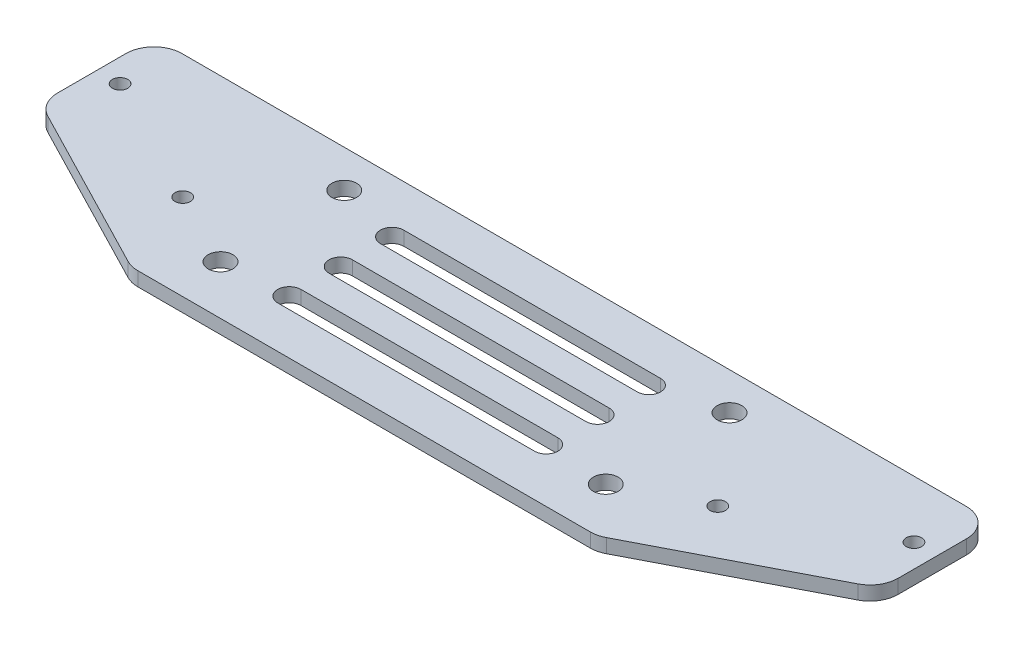
SolidWorks part; units mm, degrees
material "A-玻璃纤维"
ref_plane "前视基准面" through (0, 0, 0) normal (0, 0, 1) x (1, 0, 0)
ref_plane "上视基准面" through (0, 0, 0) normal (0, 1, 0) x (1, 0, 0)
ref_plane "右视基准面" through (0, 0, 0) normal (1, 0, 0) x (0, 0, -1)
sketch "草图1" plane through (0, 0, 0) normal (0, 1, 0) x (1, 0, 0)
  line L0 (0, 13.25) -> (0, -13.25) construction
  line L1 (-41.25, 13.25) -> (41.25, 13.25) construction
  line L2 (-41.25, 13.25) -> (-41.25, -13.25) construction
  line L3 (-41.25, -13.25) -> (41.25, -13.25) construction
  line L4 (41.25, 13.25) -> (41.25, -13.25) construction
  line L5 (-41.25, 13.25) -> (41.25, -13.25) construction
  line L6 (-41.25, -13.25) -> (41.25, 13.25) construction
  line L8 (-90, 21.25) -> (90, 21.25)
  line L9 (-90, 21.25) -> (-90, -23.75)
  line L10 (-90, -23.75) -> (90, -23.75)
  line L11 (90, 21.25) -> (90, -23.75)
  line L12 (-90, 21.25) -> (90, -23.75) construction
  line L13 (-90, -23.75) -> (90, 21.25) construction
  circle A0 centre (-41.25, 13.25) radius 2.65
  circle A1 centre (41.25, 13.25) radius 2.65
  circle A2 centre (-41.25, -13.25) radius 2.65
  circle A3 centre (41.25, -13.25) radius 2.65
  point P0 (0, 0)
  point P12 (0, -1.25)
  dimension "D1" = 5.3
  dimension "D2" = 26.5
  dimension "D3" = 82.5
  dimension "D4" = 8
  dimension "D5" = 45
  dimension "D6" = 180
extrude "凸台-拉伸1" add sketch "草图1" along normal blind 3
sketch "草图2" plane through (0, 3, 0) normal (0, 1, 0) x (1, 0, 0)
  line L0 (0, 21.25) -> (0, -23.75) construction
  line L1 (90, 21.25) -> (-90, 21.25) construction
  line L2 (-90, -23.75) -> (90, -23.75) construction
  circle A0 centre (-85, 9) radius 1.65
  circle A1 centre (85, 9) radius 1.65
  circle A2 centre (-57.3, -5.3) radius 1.65
  circle A3 centre (57.3, -5.3) radius 1.65
  circle A4 centre (-41.25, 13.25) radius 2.65 construction
  dimension "D1" = 170
  dimension "D2" = 3.3
  dimension "D3" = 114.6
  dimension "D4" = 14.3
  dimension "D5" = 4.25
extrude "切除-拉伸1" cut sketch "草图2" against normal blind 3
sketch "草图3" plane through (0, 3, 0) normal (0, 1, 0) x (1, 0, 0)
  line L0 (-90, -3.0489) -> (-90, -23.75)
  line L1 (-90, 21.25) -> (-90, -23.75) construction
  line L2 (-90, -23.75) -> (-49.9006, -23.75)
  line L3 (-90, -23.75) -> (90, -23.75) construction
  line L4 (-49.9006, -23.75) -> (-90, -3.0489)
  line L5 (0, 21.25) -> (0, -23.75) construction
  line L6 (90, 21.25) -> (-90, 21.25) construction
  line L7 (90, -23.75) -> (49.9006, -23.75)
  line L8 (90, -3.0489) -> (90, -23.75)
  line L9 (49.9006, -23.75) -> (90, -3.0489)
  line L10 (-85, 9) -> (-57.3, -5.3) construction
  dimension "D1" = 13
extrude "切除-拉伸2" cut sketch "草图3" against normal blind 3
fillet "圆角1" radius 6 6 edges at (49.9006, 1.5, 23.75) (90, 1.5, 3.0489) (90, 1.5, -21.25) (-90, 1.5, -21.25) (-49.9006, 1.5, 23.75) (-90, 1.5, 3.0489)
sketch "草图4" plane through (0, 3, 0) normal (0, 1, 0) x (1, 0, 0)
  line L0 (0, 21.25) -> (0, -23.75) construction
  line L1 (84, 21.25) -> (-84, 21.25) construction
  line L2 (-48.4433, -23.75) -> (48.4433, -23.75) construction
  line L3 (-27.5, 9.75) -> (27.5, 9.75) construction
  line L4 (-27.5, 12.25) -> (27.5, 12.25)
  line L5 (-27.5, 7.25) -> (27.5, 7.25)
  line L6 (-27.5, -1.25) -> (27.5, -1.25) construction
  line L7 (-27.5, 1.25) -> (27.5, 1.25)
  line L8 (-27.5, -3.75) -> (27.5, -3.75)
  line L9 (-27.5, -12.25) -> (27.5, -12.25) construction
  line L10 (-27.5, -9.75) -> (27.5, -9.75)
  line L11 (-27.5, -14.75) -> (27.5, -14.75)
  arc A0 (-27.5, 12.25) -> (-27.5, 7.25) centre (-27.5, 9.75) ccw
  arc A1 (27.5, 7.25) -> (27.5, 12.25) centre (27.5, 9.75) ccw
  arc A2 (-27.5, 1.25) -> (-27.5, -3.75) centre (-27.5, -1.25) ccw
  arc A3 (27.5, -3.75) -> (27.5, 1.25) centre (27.5, -1.25) ccw
  arc A4 (-27.5, -9.75) -> (-27.5, -14.75) centre (-27.5, -12.25) ccw
  arc A5 (27.5, -14.75) -> (27.5, -9.75) centre (27.5, -12.25) ccw
  point P8 (0, 9.75)
  point P14 (0, -1.25)
  point P21 (0, -12.25)
  dimension "D1" = 5
  dimension "D2" = 9
  dimension "D3" = 9
  dimension "D4" = 55
  dimension "D5" = 11
extrude "切除-拉伸3" cut sketch "草图4" against normal blind 3
